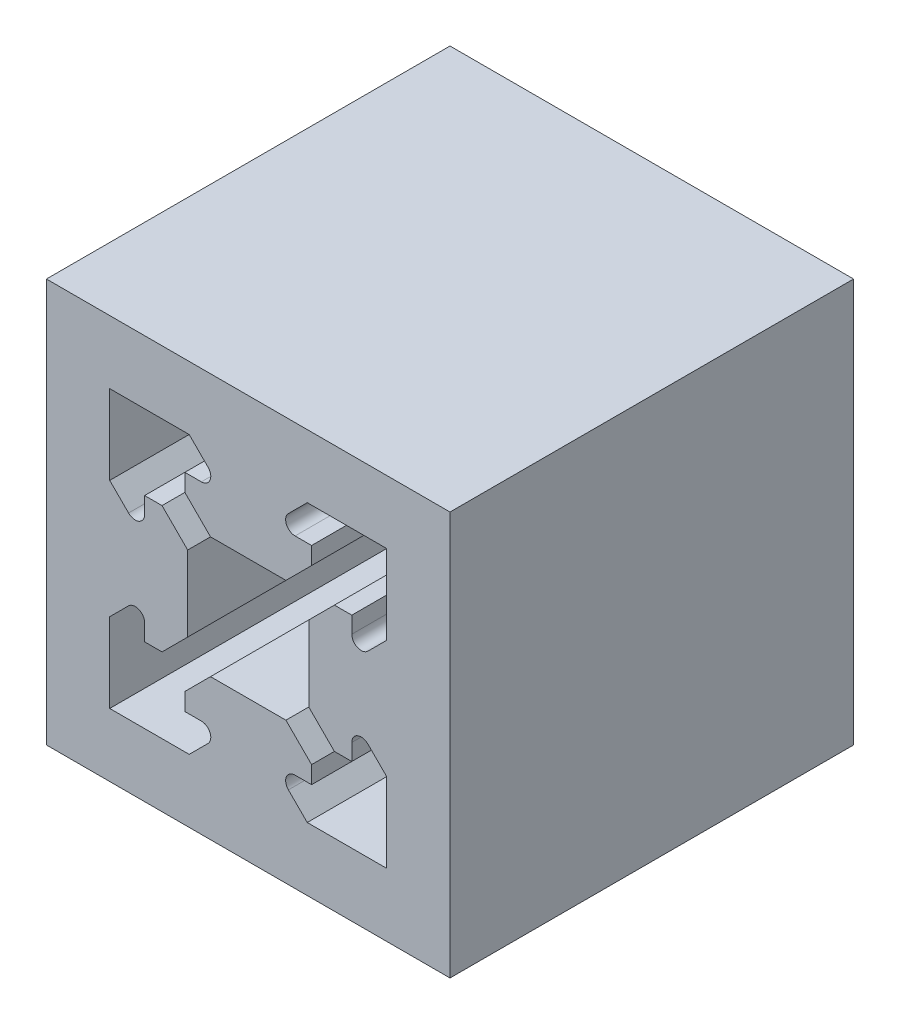
SolidWorks part; units mm, degrees
ref_plane "Front Plane" through (0, 0, 0) normal (0, 0, 1) x (1, 0, 0)
ref_plane "Top Plane" through (0, 0, 0) normal (0, 1, 0) x (1, 0, 0)
ref_plane "Right Plane" through (0, 0, 0) normal (1, 0, 0) x (0, 0, -1)
sketch "Sketch1" plane through (0, 0, 0) normal (0, 0, 1) x (1, 0, 0)
  line L0 (17.8029, 19.5) -> (12.1971, 19.5)
  line L1 (0, 0) -> (30, 0)
  line L2 (0, 0) -> (0, 30)
  line L3 (0, 30) -> (30, 30)
  line L4 (30, 0) -> (30, 30)
  line L5 (12.1971, 19.5) -> (10.2899, 21.4071)
  line L6 (10.2899, 21.4071) -> (10.2899, 22.7)
  line L7 (10.2899, 22.7) -> (11.5172, 22.7)
  line L8 (12.0121, 23.895) -> (10.6121, 25.295)
  line L9 (4.705, 19.3879) -> (6.105, 17.9879)
  line L10 (7.3, 18.4828) -> (7.3, 19.7101)
  line L11 (7.3, 19.7101) -> (8.5929, 19.7101)
  line L12 (8.5929, 19.7101) -> (10.5, 17.8029)
  line L13 (10.5, 17.8029) -> (10.5, 12.1971)
  line L14 (10.5, 12.1971) -> (8.5929, 10.2899)
  line L15 (8.5929, 10.2899) -> (7.3, 10.2899)
  line L16 (7.3, 10.2899) -> (7.3, 11.5172)
  line L17 (6.105, 12.0121) -> (4.705, 10.6121)
  line L18 (10.6121, 4.705) -> (12.0121, 6.105)
  line L19 (11.5172, 7.3) -> (10.2899, 7.3)
  line L20 (10.2899, 7.3) -> (10.2899, 8.5929)
  line L21 (10.2899, 8.5929) -> (12.1971, 10.5)
  line L22 (12.1971, 10.5) -> (17.8029, 10.5)
  line L23 (10.6121, 4.705) -> (4.705, 4.705)
  line L24 (4.705, 4.705) -> (4.705, 10.6121)
  line L25 (4.705, 19.3879) -> (4.705, 25.295)
  line L26 (4.705, 25.295) -> (10.6121, 25.295)
  line L27 (15, 30.6357) -> (15, 0.6357) construction
  line L28 (25.295, 25.295) -> (19.3879, 25.295)
  line L29 (25.295, 19.3879) -> (25.295, 25.295)
  line L30 (25.295, 4.705) -> (25.295, 10.6121)
  line L31 (19.3879, 4.705) -> (25.295, 4.705)
  line L32 (19.7101, 8.5929) -> (17.8029, 10.5)
  line L33 (19.7101, 7.3) -> (19.7101, 8.5929)
  line L34 (18.4828, 7.3) -> (19.7101, 7.3)
  line L35 (19.3879, 4.705) -> (17.9879, 6.105)
  line L36 (23.895, 12.0121) -> (25.295, 10.6121)
  line L37 (22.7, 10.2899) -> (22.7, 11.5172)
  line L38 (21.4071, 10.2899) -> (22.7, 10.2899)
  line L39 (19.5, 12.1971) -> (21.4071, 10.2899)
  line L40 (19.5, 17.8029) -> (19.5, 12.1971)
  line L41 (21.4071, 19.7101) -> (19.5, 17.8029)
  line L42 (22.7, 19.7101) -> (21.4071, 19.7101)
  line L43 (22.7, 18.4828) -> (22.7, 19.7101)
  line L44 (25.295, 19.3879) -> (23.895, 17.9879)
  line L45 (17.9879, 23.895) -> (19.3879, 25.295)
  line L46 (19.7101, 22.7) -> (18.4828, 22.7)
  line L47 (19.7101, 21.4071) -> (19.7101, 22.7)
  line L48 (17.8029, 19.5) -> (19.7101, 21.4071)
  arc A0 (17.9879, 6.105) -> (18.4828, 7.3) centre (18.4828, 6.6) cw
  arc A1 (11.5172, 22.7) -> (12.0121, 23.895) centre (11.5172, 23.4) ccw
  arc A2 (22.7, 11.5172) -> (23.895, 12.0121) centre (23.4, 11.5172) cw
  arc A3 (23.895, 17.9879) -> (22.7, 18.4828) centre (23.4, 18.4828) cw
  arc A4 (6.105, 17.9879) -> (7.3, 18.4828) centre (6.6, 18.4828) ccw
  arc A5 (7.3, 11.5172) -> (6.105, 12.0121) centre (6.6, 11.5172) ccw
  arc A6 (18.4828, 22.7) -> (17.9879, 23.895) centre (18.4828, 23.4) cw
  arc A7 (12.0121, 6.105) -> (11.5172, 7.3) centre (11.5172, 6.6) ccw
  point P5 (15, 19.5)
  point P16 (10.5, 15)
  dimension "D9" = 0.7
  dimension "D18" = 0.7
  dimension "D33" = 0.7
  dimension "D1" = 30
  dimension "D2" = 30
  dimension "D3" = 5.6059
  dimension "D4" = 2.6971
  dimension "D5" = 1.2929
  dimension "D6" = 2.595
  dimension "D7" = 135
  dimension "D8" = 1.2934
  dimension "D10" = 1.9799
  dimension "D11" = 135
  dimension "D12" = 1.2272
  dimension "D13" = 5.6059
  dimension "D14" = 2.6971
  dimension "D15" = 1.2929
  dimension "D16" = 1.2272
  dimension "D17" = 1.2934
  dimension "D19" = 1.9799
  dimension "D20" = 225
  dimension "D21" = 5.9071
  dimension "D22" = 135
  dimension "D23" = 90
  dimension "D24" = 135
  dimension "D25" = 2.595
  dimension "D26" = 135
  dimension "D27" = 135
  dimension "D28" = 1.2934
  dimension "D29" = 5.9071
  dimension "D30" = 1.9799
  dimension "D31" = 135
  dimension "D32" = 1.2934
  dimension "D34" = 1.2272
  dimension "D35" = 90
  dimension "D36" = 135
  dimension "D37" = 1.2929
  dimension "D38" = 2.595
  dimension "D39" = 2.6971
  dimension "D40" = 5.6059
  dimension "D41" = 5.9071
  dimension "D42" = 15
  dimension "D43" = 15
extrude "Boss-Extrude1" add sketch "Sketch1" along normal blind 30
